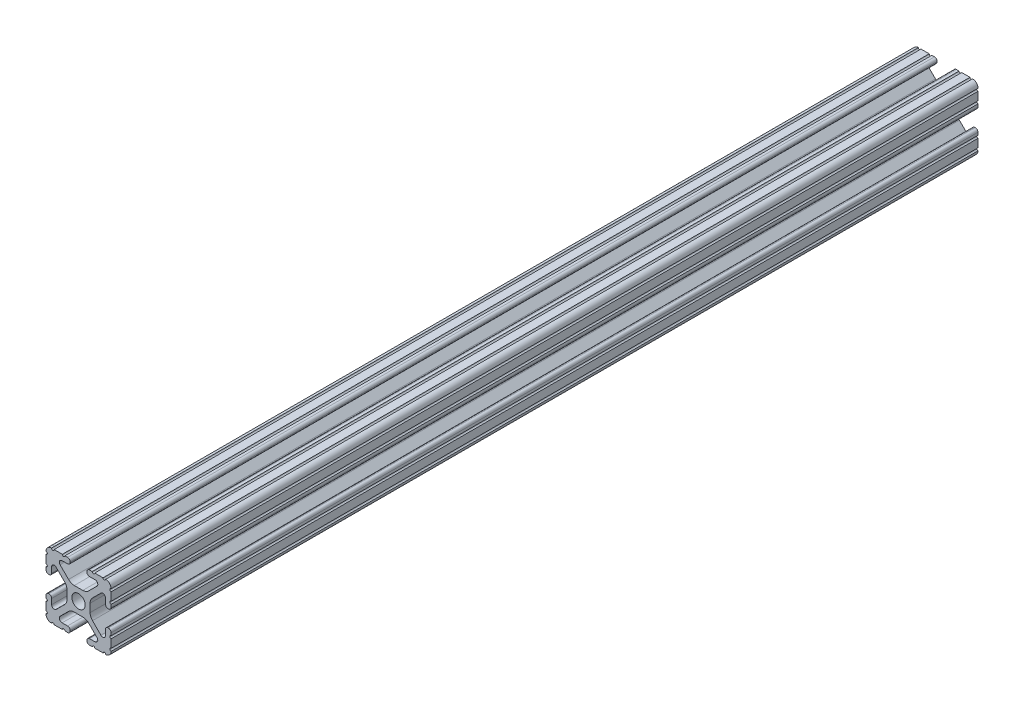
SolidWorks part; units mm, degrees
ref_plane "Front" through (0, 0, 0) normal (0, 0, 1) x (1, 0, 0)
ref_plane "Top" through (0, 0, 0) normal (0, 1, 0) x (1, 0, 0)
ref_plane "Right" through (0, 0, 0) normal (1, 0, 0) x (0, 0, -1)
sketch "Sketch1" plane through (0, 0, 0) normal (0, 0, 1) x (1, 0, 0)
  line L0 (-7.5107, 9.4563) -> (7.5107, 9.4563) construction
  line L1 (-7.4968, -9.4098) -> (7.4968, -9.4098) construction
  line L88 (-7.1797, -8.6452) -> (-3.9523, -5.4237)
  line L89 (-1.7093, -4.4958) -> (1.7093, -4.4958)
  line L90 (3.9523, -5.4237) -> (7.1797, -8.6452)
  line L91 (6.4164, -10.4902) -> (4.2875, -10.4902)
  line L92 (3.2385, -11.5392) -> (3.2385, -11.651)
  line L93 (4.2875, -12.7) -> (5.3171, -12.7)
  line L94 (6.3331, -12.7) -> (9.5504, -12.7)
  line L95 (12.7, -9.5504) -> (12.7, -6.3331)
  line L96 (12.7, -5.3171) -> (12.7, -4.2875)
  line L97 (11.651, -3.2385) -> (11.5392, -3.2385)
  line L98 (10.4902, -4.2875) -> (10.4902, -6.4021)
  line L99 (8.7371, -7.1294) -> (5.441, -3.8408)
  line L100 (4.5085, -1.5932) -> (4.5085, 1.5932)
  line L101 (5.441, 3.8408) -> (8.7371, 7.1294)
  line L102 (10.4902, 6.4021) -> (10.4902, 4.2875)
  line L103 (11.5392, 3.2385) -> (11.651, 3.2385)
  line L104 (12.7, 4.2875) -> (12.7, 5.3171)
  line L105 (12.7, 6.3331) -> (12.7, 9.5504)
  line L106 (9.5504, 12.7) -> (6.3331, 12.7)
  line L107 (5.3171, 12.7) -> (4.2875, 12.7)
  line L108 (3.2385, 11.651) -> (3.2385, 11.5392)
  line L109 (4.2875, 10.4902) -> (6.4768, 10.4902)
  line L110 (7.207, 8.7244) -> (3.8983, 5.4232)
  line L111 (1.6558, 4.4958) -> (-1.6558, 4.4958)
  line L112 (-3.8983, 5.4232) -> (-7.207, 8.7244)
  line L113 (-6.4768, 10.4902) -> (-4.2875, 10.4902)
  line L114 (-3.2385, 11.5392) -> (-3.2385, 11.651)
  line L115 (-4.2875, 12.7) -> (-5.3171, 12.7)
  line L116 (-6.3331, 12.7) -> (-9.5504, 12.7)
  line L117 (-12.7, 9.5504) -> (-12.7, 6.3331)
  line L118 (-12.7, 5.3171) -> (-12.7, 4.2875)
  line L119 (-11.651, 3.2385) -> (-11.5392, 3.2385)
  line L120 (-10.4902, 4.2875) -> (-10.4902, 6.4021)
  line L121 (-8.7371, 7.1294) -> (-5.441, 3.8408)
  line L122 (-4.5085, 1.5932) -> (-4.5085, -1.5932)
  line L123 (-5.441, -3.8408) -> (-8.7371, -7.1294)
  line L124 (-10.4902, -6.4021) -> (-10.4902, -4.2875)
  line L125 (-11.5392, -3.2385) -> (-11.651, -3.2385)
  line L126 (-12.7, -4.2875) -> (-12.7, -5.3171)
  line L127 (-12.7, -6.3331) -> (-12.7, -9.5504)
  line L128 (-9.5504, -12.7) -> (-6.3331, -12.7)
  line L129 (-5.3171, -12.7) -> (-4.2875, -12.7)
  line L130 (-3.2385, -11.651) -> (-3.2385, -11.5392)
  line L131 (-4.2875, -10.4902) -> (-6.4164, -10.4902)
  circle A1 centre (0, 0) radius 2.6035
  arc A104 (-7.1797, -8.6452) -> (-6.4164, -10.4902) centre (-6.4164, -9.4098) ccw
  arc A105 (-1.7093, -4.4958) -> (-3.9523, -5.4237) centre (-1.7093, -7.6708) ccw
  arc A106 (3.9523, -5.4237) -> (1.7093, -4.4958) centre (1.7093, -7.6708) ccw
  arc A107 (6.4164, -10.4902) -> (7.1797, -8.6452) centre (6.4164, -9.4098) ccw
  arc A108 (4.2875, -10.4902) -> (3.2385, -11.5392) centre (4.2875, -11.5392) ccw
  arc A109 (3.2385, -11.651) -> (4.2875, -12.7) centre (4.2875, -11.651) ccw
  arc A110 (6.3331, -12.7) -> (5.3171, -12.7) centre (5.8251, -12.7) ccw
  arc A111 (10.5664, -12.6998) -> (9.5504, -12.7) centre (10.0584, -12.7) ccw
  arc A112 (10.5664, -12.6998) -> (12.6998, -10.5664) centre (10.5918, -10.5918) ccw
  arc A113 (12.7, -9.5504) -> (12.6998, -10.5664) centre (12.7, -10.0584) ccw
  arc A114 (12.7, -5.3171) -> (12.7, -6.3331) centre (12.7, -5.8251) ccw
  arc A115 (12.7, -4.2875) -> (11.651, -3.2385) centre (11.651, -4.2875) ccw
  arc A116 (11.5392, -3.2385) -> (10.4902, -4.2875) centre (11.5392, -4.2875) ccw
  arc A117 (8.7371, -7.1294) -> (10.4902, -6.4021) centre (9.4628, -6.4021) ccw
  arc A118 (4.5085, -1.5932) -> (5.441, -3.8408) centre (7.6835, -1.5932) ccw
  arc A119 (5.441, 3.8408) -> (4.5085, 1.5932) centre (7.6835, 1.5932) ccw
  arc A120 (10.4902, 6.4021) -> (8.7371, 7.1294) centre (9.4628, 6.4021) ccw
  arc A121 (10.4902, 4.2875) -> (11.5392, 3.2385) centre (11.5392, 4.2875) ccw
  arc A122 (11.651, 3.2385) -> (12.7, 4.2875) centre (11.651, 4.2875) ccw
  arc A123 (12.7, 6.3331) -> (12.7, 5.3171) centre (12.7, 5.8251) ccw
  arc A124 (12.6998, 10.5664) -> (12.7, 9.5504) centre (12.7, 10.0584) ccw
  arc A125 (12.6998, 10.5664) -> (10.5664, 12.6998) centre (10.5918, 10.5918) ccw
  arc A126 (9.5504, 12.7) -> (10.5664, 12.6998) centre (10.0584, 12.7) ccw
  arc A127 (5.3171, 12.7) -> (6.3331, 12.7) centre (5.8251, 12.7) ccw
  arc A128 (4.2875, 12.7) -> (3.2385, 11.651) centre (4.2875, 11.651) ccw
  arc A129 (3.2385, 11.5392) -> (4.2875, 10.4902) centre (4.2875, 11.5392) ccw
  arc A130 (7.207, 8.7244) -> (6.4768, 10.4902) centre (6.4768, 9.4563) ccw
  arc A131 (1.6558, 4.4958) -> (3.8983, 5.4232) centre (1.6558, 7.6708) ccw
  arc A132 (-3.8983, 5.4232) -> (-1.6558, 4.4958) centre (-1.6558, 7.6708) ccw
  arc A133 (-6.4768, 10.4902) -> (-7.207, 8.7244) centre (-6.4768, 9.4563) ccw
  arc A134 (-4.2875, 10.4902) -> (-3.2385, 11.5392) centre (-4.2875, 11.5392) ccw
  arc A135 (-3.2385, 11.651) -> (-4.2875, 12.7) centre (-4.2875, 11.651) ccw
  arc A136 (-6.3331, 12.7) -> (-5.3171, 12.7) centre (-5.8251, 12.7) ccw
  arc A137 (-10.5664, 12.6998) -> (-9.5504, 12.7) centre (-10.0584, 12.7) ccw
  arc A138 (-10.5664, 12.6998) -> (-12.6998, 10.5664) centre (-10.5918, 10.5918) ccw
  arc A139 (-12.7, 9.5504) -> (-12.6998, 10.5664) centre (-12.7, 10.0584) ccw
  arc A140 (-12.7, 5.3171) -> (-12.7, 6.3331) centre (-12.7, 5.8251) ccw
  arc A141 (-12.7, 4.2875) -> (-11.651, 3.2385) centre (-11.651, 4.2875) ccw
  arc A142 (-11.5392, 3.2385) -> (-10.4902, 4.2875) centre (-11.5392, 4.2875) ccw
  arc A143 (-8.7371, 7.1294) -> (-10.4902, 6.4021) centre (-9.4628, 6.4021) ccw
  arc A144 (-4.5085, 1.5932) -> (-5.441, 3.8408) centre (-7.6835, 1.5932) ccw
  arc A145 (-5.441, -3.8408) -> (-4.5085, -1.5932) centre (-7.6835, -1.5932) ccw
  arc A146 (-10.4902, -6.4021) -> (-8.7371, -7.1294) centre (-9.4628, -6.4021) ccw
  arc A147 (-10.4902, -4.2875) -> (-11.5392, -3.2385) centre (-11.5392, -4.2875) ccw
  arc A148 (-11.651, -3.2385) -> (-12.7, -4.2875) centre (-11.651, -4.2875) ccw
  arc A149 (-12.7, -6.3331) -> (-12.7, -5.3171) centre (-12.7, -5.8251) ccw
  arc A150 (-12.6998, -10.5664) -> (-12.7, -9.5504) centre (-12.7, -10.0584) ccw
  arc A151 (-12.6998, -10.5664) -> (-10.5664, -12.6998) centre (-10.5918, -10.5918) ccw
  arc A152 (-9.5504, -12.7) -> (-10.5664, -12.6998) centre (-10.0584, -12.7) ccw
  arc A153 (-5.3171, -12.7) -> (-6.3331, -12.7) centre (-5.8251, -12.7) ccw
  arc A154 (-4.2875, -12.7) -> (-3.2385, -11.651) centre (-4.2875, -11.651) ccw
  arc A155 (-3.2385, -11.5392) -> (-4.2875, -10.4902) centre (-4.2875, -11.5392) ccw
extrude "Boss-Extrude1" add sketch "Sketch1" along normal mid plane 914.4
sketch "Sketch3" plane through (-12.7, 0, 0) normal (-1, 0, 0) x (0, 0, 1)
  line L0 (-203.2, -25.4) -> (-203.2, 21.1581) construction
  line L1 (-203.2, -27.5528) -> (-203.2, 21.1581)
  line L2 (-203.2, 21.1581) -> (-461.0909, 21.1581)
  line L3 (-461.0909, 21.1581) -> (-461.0909, -25.4)
  line L4 (-461.0909, -25.4) -> (-203.2, -27.5528)
extrude "Cut-Extrude2" cut sketch "Sketch3" against normal blind 26.924 and the other way blind 4.318
sketch "Sketch4" plane through (12.7, 0, 0) normal (1, 0, 0) x (0, 0, -1)
  line L0 (-118.942, -15.1901) -> (-118.942, 20.2728) construction
  line L1 (-118.942, -15.1901) -> (-118.942, 15.0072)
  line L2 (-118.942, 15.0072) -> (205.9683, 15.0072)
  line L3 (205.9683, 15.0072) -> (205.9683, -15.1901)
  line L4 (205.9683, -15.1901) -> (-118.942, -15.1901)
  point P5 (-115.1801, 20.3269)
  point P6 (-118.942, 20.2728)
extrude "Cut-Extrude3" cut sketch "Sketch4" along normal through all and the other way through all
